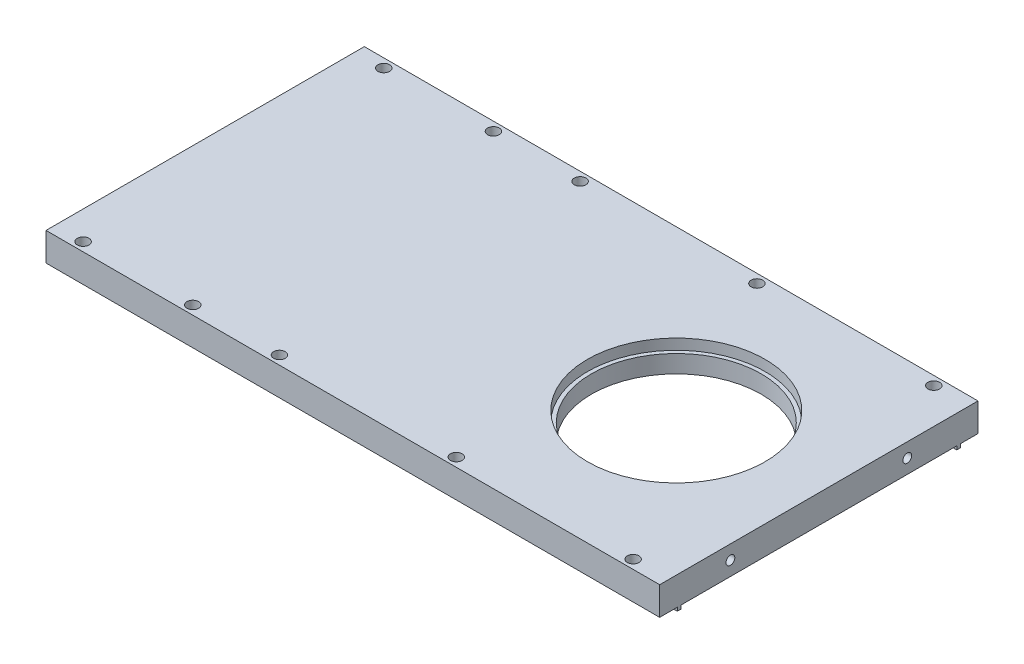
SolidWorks part; units mm, degrees
ref_plane "Front Plane" through (0, 0, 0) normal (0, 0, 1) x (1, 0, 0)
ref_plane "Top Plane" through (0, 0, 0) normal (0, 1, 0) x (1, 0, 0)
ref_plane "Right Plane" through (0, 0, 0) normal (1, 0, 0) x (0, 0, -1)
sketch "Sketch1" plane through (0, 0, 0) normal (0, 0, 1) x (1, 0, 0)
  line L0 (0, 0) -> (0, 5)
  line L5 (0, 5) -> (53.5, 5)
  line L6 (53.5, 5) -> (53.5, -14)
  line L7 (53.5, -14) -> (217, -14)
  line L8 (217, -14) -> (217, -22)
  line L9 (217, -22) -> (43.5, -22)
  line L10 (43.5, -22) -> (43.5, 0)
  line L11 (43.5, 0) -> (0, 0)
  line L12 (43.5, 0) -> (53.5, 0) construction
  point P0 (0, 2.5)
  dimension "D1" = 5
  dimension "D2" = 217
  dimension "D3" = 10
  dimension "D4" = 22
  dimension "D5" = 163.5
  dimension "D6" = 8
extrude "Boss-Extrude1" add sketch "Sketch1" along normal blind 90
sketch "Sketch2" plane through (0, -14, 0) normal (0, 1, 0) x (1, 0, 0)
  line L0 (217, -90) -> (217, 0) construction
  circle A0 centre (176.7, -45) radius 24
  point P5 (217, -45)
  dimension "D1" = 48
  dimension "D2" = 40.3
extrude "Cut-Extrude1" cut sketch "Sketch2" against normal through all
sketch "Sketch3" plane through (0, -14, 0) normal (0, 1, 0) x (1, 0, 0)
  circle A0 centre (176.7, -45) radius 25.1
  dimension "D1" = 50.2
extrude "Cut-Extrude2" cut sketch "Sketch3" against normal blind 3
sketch "Sketch4" plane through (0, -22, 0) normal (0, -1, 0) x (1, 0, 0)
  line L1 (73.5, 84) -> (217, 84)
  line L2 (73.5, 84) -> (73.5, 85)
  line L3 (73.5, 85) -> (217, 85)
  line L4 (217, 84) -> (217, 85)
  line L5 (217, 90) -> (217, 0) construction
  line L6 (43.5, 90) -> (217, 90) construction
  line L7 (73.5, 6) -> (217, 6)
  line L8 (73.5, 6) -> (73.5, 5)
  line L9 (73.5, 5) -> (217, 5)
  line L10 (217, 6) -> (217, 5)
  line L11 (43.5, 0) -> (217, 0) construction
  line L12 (43.5, 90) -> (43.5, 0) construction
  dimension "D1" = 1
  dimension "D2" = 5
  dimension "D3" = 5
  dimension "D4" = 30
extrude "Boss-Extrude2" add sketch "Sketch4" along normal blind 1
sketch "Sketch5" plane through (0, 0, 0) normal (0, -1, 0) x (1, 0, 0)
  line L0 (73.5, 84) -> (217, 84) construction
  line L1 (33.5, 85) -> (23.5, 85)
  line L2 (33.5, 85) -> (33.5, 84)
  line L3 (33.5, 84) -> (23.5, 84)
  line L4 (23.5, 85) -> (23.5, 84)
  line L5 (73.5, 5) -> (217, 5) construction
  line L6 (33.5, 6) -> (23.5, 6)
  line L7 (33.5, 6) -> (33.5, 5)
  line L8 (33.5, 5) -> (23.5, 5)
  line L9 (23.5, 6) -> (23.5, 5)
  line L10 (43.5, 90) -> (43.5, 0) construction
  dimension "D1" = 10
  dimension "D2" = 10
extrude "Boss-Extrude3" add sketch "Sketch5" along normal blind 2
ref_plane "Plane1" through (0, 15, 0) normal (0, 1, 0) x (1, 0, 0)
sketch "Sketch6" plane through (0, 15, 0) normal (0, 1, 0) x (1, 0, 0)
  line L1 (51.5, -87.5) -> (82.5, -87.5) construction
  line L2 (51.5, -87.5) -> (51.5, -2.5) construction
  line L3 (51.5, -2.5) -> (82.5, -2.5) construction
  line L4 (82.5, -87.5) -> (82.5, -2.5) construction
  line L5 (51.5, -87.5) -> (82.5, -2.5) construction
  line L6 (51.5, -2.5) -> (82.5, -87.5) construction
  line L7 (107, -87.5) -> (207, -87.5) construction
  line L8 (107, -87.5) -> (107, -2.5) construction
  line L9 (107, -2.5) -> (207, -2.5) construction
  line L10 (207, -87.5) -> (207, -2.5) construction
  line L11 (107, -87.5) -> (207, -2.5) construction
  line L12 (107, -2.5) -> (207, -87.5) construction
  line L14 (207, -2.5) -> (217, -2.5) construction
  line L15 (217, -90) -> (217, 0) construction
  line L16 (207, -2.5) -> (207, 0) construction
  line L17 (217, 0) -> (53.5, 0) construction
  line L18 (51.5, -87.5) -> (0, -87.5) construction
  line L19 (0, -90) -> (0, 0) construction
  line L20 (51.5, -87.5) -> (51.5, -90) construction
  line L21 (53.5, -90) -> (0, -90) construction
  circle A0 centre (51.5, -2.5) radius 1.65
  circle A1 centre (82.5, -2.5) radius 1.65
  circle A2 centre (51.5, -87.5) radius 1.65
  circle A3 centre (82.5, -87.5) radius 1.65
  circle A4 centre (107, -87.5) radius 1.65
  circle A5 centre (157, -87.5) radius 1.65
  circle A6 centre (207, -87.5) radius 1.65
  circle A7 centre (107, -2.5) radius 1.65
  circle A8 centre (157, -2.5) radius 1.65
  circle A9 centre (207, -2.5) radius 1.65
  point P0 (67, -45)
  point P5 (157, -45)
  dimension "D6" = 3.3
  dimension "D1" = 2.5
  dimension "D2" = 10
  dimension "D3" = 51.5
  dimension "D4" = 31
  dimension "D5" = 100
extrude "Cut-Extrude3" cut sketch "Sketch6" against normal through all
hole_wizard "M3 Tapped Hole1" positions "Sketch7" profile "Sketch8" tap size "M3" standard "ISO"
sketch "Sketch7" plane through (217, 0, 0) normal (1, 0, 0) x (0, 0, -1)
  line L0 (-70, -18) -> (-90, -18) construction
  line L1 (-90, -22) -> (-90, -14) construction
  line L3 (-70, -18) -> (-20, -18) construction
  line L5 (-45, -18) -> (-45, -14) construction
  line L6 (-90, -14) -> (0, -14) construction
  point P0 (-70, -18)
  point P2 (-20, -18)
  dimension "D1" = 50
sketch "Sketch8" plane through (217, -18, 70) normal (0, 1, 0) x (0, 0, -1)
  line L0 (0, 0) -> (0, 9.2511)
  line L1 (0, 9.2511) -> (1.25, 8.5)
  line L2 (1.25, 8.5) -> (1.25, 0)
  line L5 (1.25, 0) -> (0, 0)
  line L10 (0, 9.2511) -> (-1.25, 8.5) construction
  line L11 (0, -6.35) -> (0, 107.95) construction
  dimension "Tap Drill Dia." = 2.5
  dimension "Tap Drill Depth" = 8.5
  dimension "Drill Angle" = 118
cosmetic thread "Hole Thread1" parameters "D1"=6, "D2"=3
cosmetic thread "Hole Thread2" parameters "D1"=6, "D2"=3
sketch "草图1" plane through (0, 0, 90) normal (0, 0, 1) x (1, 0, 0)
  line L1 (0, 5) -> (53.5, 5)
  line L2 (0, 5) -> (0, -14)
  line L3 (0, -14) -> (53.5, -14)
  line L4 (53.5, 5) -> (53.5, -14)
extrude "切除-拉伸1" cut sketch "草图1" against normal blind 90
